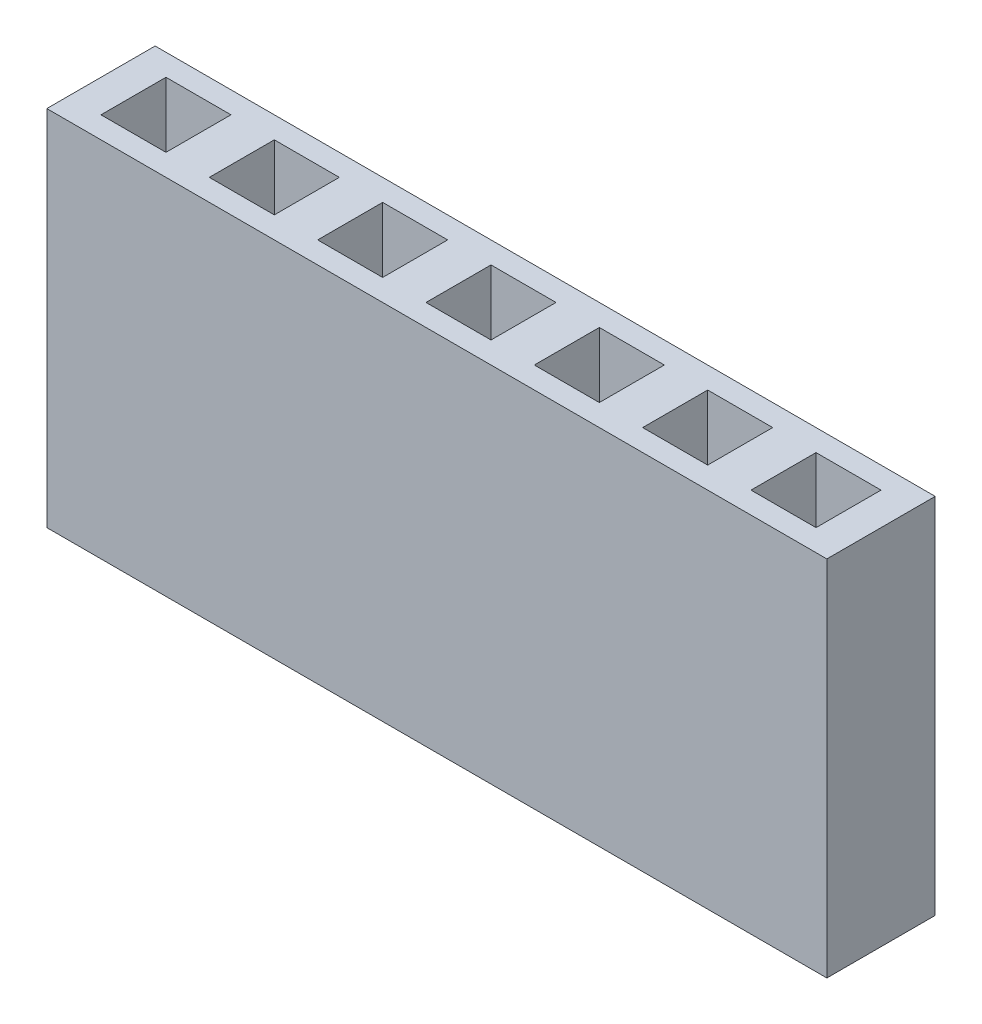
SolidWorks part; units mm, degrees
ref_plane "Front Plane" through (0, 0, 0) normal (0, 0, 1) x (1, 0, 0)
ref_plane "Top Plane" through (0, 0, 0) normal (0, 1, 0) x (1, 0, 0)
ref_plane "Right Plane" through (0, 0, 0) normal (1, 0, 0) x (0, 0, -1)
sketch "Sketch1" plane through (0, 0, 0) normal (0, 1, 0) x (1, 0, 0)
  line L1 (9.144, -1.27) -> (-9.144, -1.27)
  line L2 (9.144, -1.27) -> (9.144, 1.27)
  line L3 (9.144, 1.27) -> (-9.144, 1.27)
  line L4 (-9.144, -1.27) -> (-9.144, 1.27)
  line L5 (9.144, -1.27) -> (-9.144, 1.27) construction
  line L6 (9.144, 1.27) -> (-9.144, -1.27) construction
  point P0 (0, 0)
  dimension "D1" = 18.288
  dimension "D2" = 2.54
extrude "Boss-Extrude1" add sketch "Sketch1" along normal blind 8.509
sketch "Sketch2" plane through (0, 8.509, 0) normal (0, 1, 0) x (1, 0, 0)
  line L0 (1.778, -0.762) -> (1.778, 0.762)
  line L1 (-0.762, -0.762) -> (0.762, -0.762)
  line L2 (-0.762, -0.762) -> (-0.762, 0.762)
  line L3 (-0.762, 0.762) -> (0.762, 0.762)
  line L4 (0.762, -0.762) -> (0.762, 0.762)
  line L5 (-0.762, -0.762) -> (0.762, 0.762) construction
  line L6 (-0.762, 0.762) -> (0.762, -0.762) construction
  line L7 (1.778, -0.762) -> (3.302, -0.762)
  line L8 (3.302, -0.762) -> (3.302, 0.762)
  line L9 (1.778, 0.762) -> (3.302, 0.762)
  line L10 (4.318, -0.762) -> (4.318, 0.762)
  line L11 (4.318, -0.762) -> (5.842, -0.762)
  line L12 (5.842, -0.762) -> (5.842, 0.762)
  line L13 (4.318, 0.762) -> (5.842, 0.762)
  line L14 (6.858, -0.762) -> (6.858, 0.762)
  line L15 (6.858, -0.762) -> (8.382, -0.762)
  line L16 (8.382, -0.762) -> (8.382, 0.762)
  line L17 (6.858, 0.762) -> (8.382, 0.762)
  line L18 (-3.302, -0.762) -> (-3.302, 0.762)
  line L19 (-3.302, -0.762) -> (-1.778, -0.762)
  line L20 (-1.778, -0.762) -> (-1.778, 0.762)
  line L21 (-3.302, 0.762) -> (-1.778, 0.762)
  line L22 (-5.842, -0.762) -> (-5.842, 0.762)
  line L23 (-5.842, -0.762) -> (-4.318, -0.762)
  line L24 (-4.318, -0.762) -> (-4.318, 0.762)
  line L25 (-5.842, 0.762) -> (-4.318, 0.762)
  line L26 (-8.382, -0.762) -> (-8.382, 0.762)
  line L27 (-8.382, -0.762) -> (-6.858, -0.762)
  line L28 (-6.858, -0.762) -> (-6.858, 0.762)
  line L29 (-8.382, 0.762) -> (-6.858, 0.762)
  point P0 (0, 0)
  dimension "D1" = 1.524
  dimension "D2" = 1.524
  dimension "D3" = 4
  dimension "D4" = 4
extrude "Cut-Extrude1" cut sketch "Sketch2" against normal blind 5.9944
